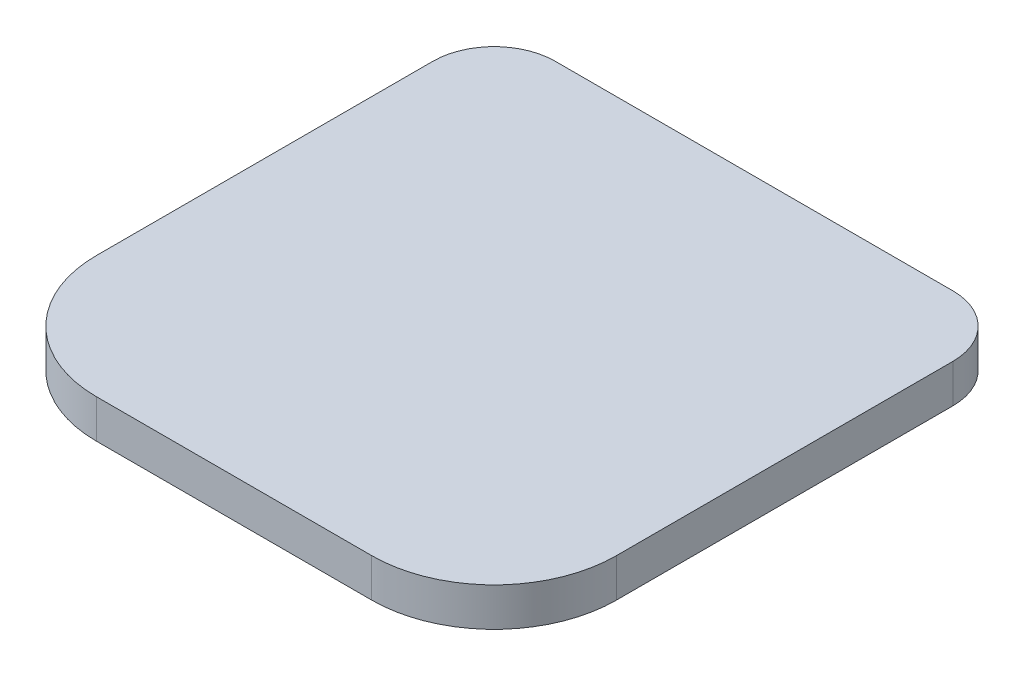
SolidWorks part; units mm, degrees
ref_plane "Front Plane" through (0, 0, 0) normal (0, 0, 1) x (1, 0, 0)
ref_plane "Top Plane" through (0, 0, 0) normal (0, 1, 0) x (1, 0, 0)
ref_plane "Right Plane" through (0, 0, 0) normal (1, 0, 0) x (0, 0, -1)
sketch "Sketch1" plane through (0, 0, 0) normal (0, 1, 0) x (1, 0, 0)
  line L1 (0, 0) -> (85, 0)
  line L2 (0, 0) -> (0, 85)
  line L3 (0, 85) -> (85, 85)
  line L4 (85, 0) -> (85, 85)
  dimension "D1" = 85
  dimension "D2" = 85
extrude "Boss-Extrude1" add sketch "Sketch1" along normal blind 6.3
fillet "Fillet1" radius 10 2 edges at (85, 3.15, -85) (0, 3.15, -85)
fillet "Fillet2" radius 20 2 edges at (0, 3.15, 0) (85, 3.15, 0)
